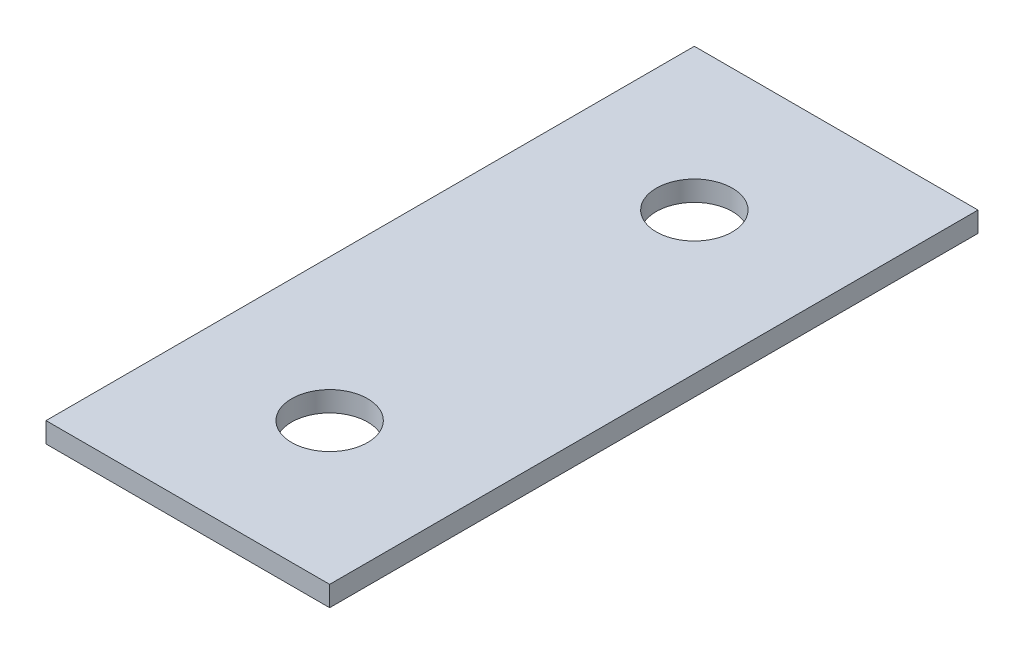
SolidWorks part; units mm, degrees
material "ASTM A36 Steel"
ref_plane "Front Plane" through (0, 0, 0) normal (0, 0, 1) x (1, 0, 0)
ref_plane "Top Plane" through (0, 0, 0) normal (0, 1, 0) x (1, 0, 0)
ref_plane "Right Plane" through (0, 0, 0) normal (1, 0, 0) x (0, 0, -1)
sketch "Sketch1" plane through (0, 0, 0) normal (0, 1, 0) x (1, 0, 0)
  line L1 (0, 0) -> (88.9, 0)
  line L2 (0, 0) -> (0, 203.2)
  line L3 (0, 203.2) -> (88.9, 203.2)
  line L4 (88.9, 0) -> (88.9, 203.2)
  circle A0 centre (44.45, 158.75) radius 11.9062
  circle A1 centre (44.45, 44.45) radius 11.9062
  dimension "D6" = 23.8125
  dimension "D1" = 203.2
  dimension "D2" = 88.9
  dimension "D3" = 44.45
  dimension "D4" = 44.45
  dimension "D5" = 44.45
extrude "Boss-Extrude1" add sketch "Sketch1" along normal blind 6.35
